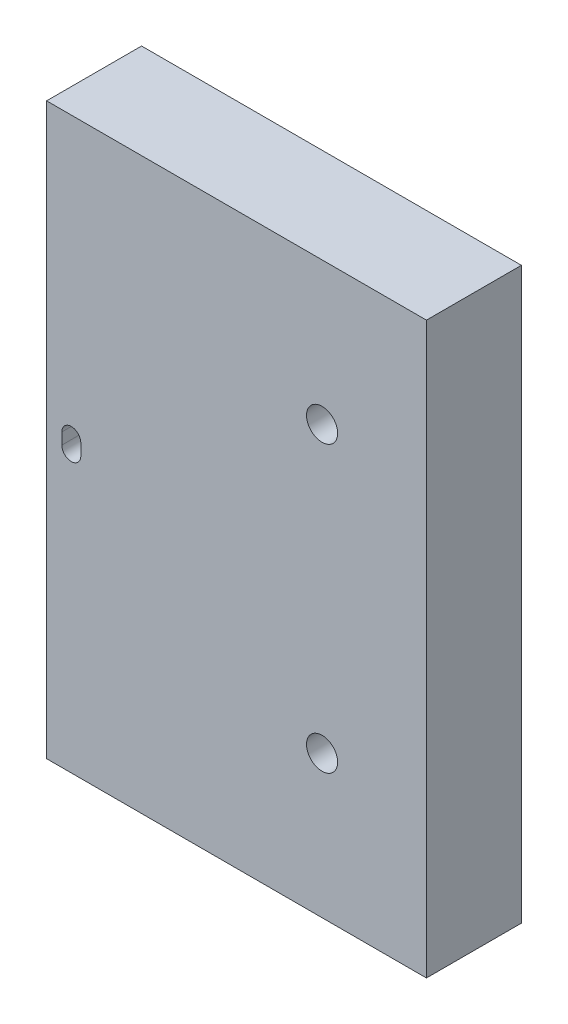
SolidWorks part; units mm, degrees
ref_plane "Front Plane" through (0, 0, 0) normal (0, 0, 1) x (1, 0, 0)
ref_plane "Top Plane" through (0, 0, 0) normal (0, 1, 0) x (1, 0, 0)
ref_plane "Right Plane" through (0, 0, 0) normal (1, 0, 0) x (0, 0, -1)
sketch "Sketch1" plane through (0, 0, 0) normal (0, 0, 1) x (1, 0, 0)
  line L1 (-12.7, -19.05) -> (12.7, -19.05)
  line L2 (-12.7, -19.05) -> (-12.7, 19.05)
  line L3 (-12.7, 19.05) -> (12.7, 19.05)
  line L4 (12.7, -19.05) -> (12.7, 19.05)
  line L5 (-12.7, -19.05) -> (12.7, 19.05) construction
  line L6 (-12.7, 19.05) -> (12.7, -19.05) construction
  point P0 (0, 0)
  dimension "D1" = 25.4
  dimension "D2" = 38.1
extrude "Boss-Extrude1" add sketch "Sketch1" along normal blind 6.35
hole_wizard "Tap Drill for #3-56 Tap1" positions "Sketch3" profile "Sketch2" hole size "#3-56" standard "ANSI Inch"
sketch "Sketch3" plane through (-12.7, 0, 0) normal (-1, 0, 0) x (0, 0, 1)
  line L0 (0, -11.775) -> (6.35, -11.775) construction
  line L1 (0, 19.05) -> (0, -19.05) construction
  line L2 (6.35, 19.05) -> (6.35, -19.05) construction
  line L4 (0, 7.225) -> (6.35, 7.225) construction
  circle A0 centre (2.85, -11.775) radius 1.5 construction
  circle A1 centre (2.85, 7.225) radius 1.5 construction
  point P0 (2.85, 7.225)
  point P2 (2.85, -11.775)
sketch "Sketch2" plane through (-12.7, 7.225, 2.85) normal (0, 1, 0) x (0, 0, 1)
  line L0 (0, 0) -> (0, 8.2457)
  line L1 (0, 8.2457) -> (1.0414, 7.62)
  line L2 (1.0414, 7.62) -> (1.0414, 0)
  line L5 (1.0414, 0) -> (0, 0)
  line L10 (0, 8.2457) -> (-1.0414, 7.62) construction
  line L11 (0, -6.35) -> (0, 107.95) construction
  dimension "Hole Dia." = 2.0828
  dimension "Hole Depth" = 7.62
  dimension "Drill Angle" = 118
sketch "Sketch4" plane through (0, 0, 6.35) normal (0, 0, 1) x (1, 0, 0)
  line L0 (-12.7, -11.775) -> (12.7, -11.775) construction
  line L1 (-12.7, 19.05) -> (-12.7, -19.05) construction
  line L2 (12.7, -19.05) -> (12.7, 19.05) construction
  line L3 (-12.7, 7.225) -> (12.7, 7.225) construction
  line L6 (-12.7, 0) -> (12.7, 0) construction
  line L8 (-10.414, -0.381) -> (-11.684, -0.381) construction
  line L9 (-10.414, -0.381) -> (-10.414, 0.381)
  line L10 (-10.414, 0.381) -> (-11.684, 0.381) construction
  line L11 (-11.684, -0.381) -> (-11.684, 0.381)
  line L12 (-10.414, -0.381) -> (-11.684, 0.381) construction
  line L13 (-10.414, 0.381) -> (-11.684, -0.381) construction
  arc A0 (-10.414, -0.381) -> (-11.684, -0.381) centre (-11.049, -0.381) cw
  arc A1 (-10.414, 0.381) -> (-11.684, 0.381) centre (-11.049, 0.381) ccw
  point P12 (-11.049, 0)
  dimension "D1" = 0.762
  dimension "D2" = 1.016
  dimension "D3" = 1.27
extrude "Cut-Extrude1" cut sketch "Sketch4" against normal through all
hole_wizard "Tap Drill for #3-56 Tap2" positions "Sketch6" profile "Sketch5" hole size "#3-56" standard "ANSI Inch"
sketch "Sketch6" plane through (0, 0, 0) normal (0, 0, 1) x (1, 0, 0)
  line L0 (2.546, 0) -> (8.896, 0) construction
  line L3 (5.721, 0) -> (5.721, 19.05) construction
  line L4 (12.7, 19.05) -> (-12.7, 19.05) construction
  line L5 (8.896, 19.05) -> (8.896, -19.05) construction
  point P12 (5.721, 9.525)
  point P15 (5.721, -9.525)
sketch "Sketch5" plane through (5.721, 9.525, 0) normal (1, 0, 0) x (0, 1, 0)
  line L0 (0, 0) -> (0, 8.2457)
  line L1 (0, 8.2457) -> (1.0414, 7.62)
  line L2 (1.0414, 7.62) -> (1.0414, 0)
  line L5 (1.0414, 0) -> (0, 0)
  line L10 (0, 8.2457) -> (-1.0414, 7.62) construction
  line L11 (0, -6.35) -> (0, 107.95) construction
  dimension "Hole Dia." = 2.0828
  dimension "Hole Depth" = 7.62
  dimension "Drill Angle" = 118
